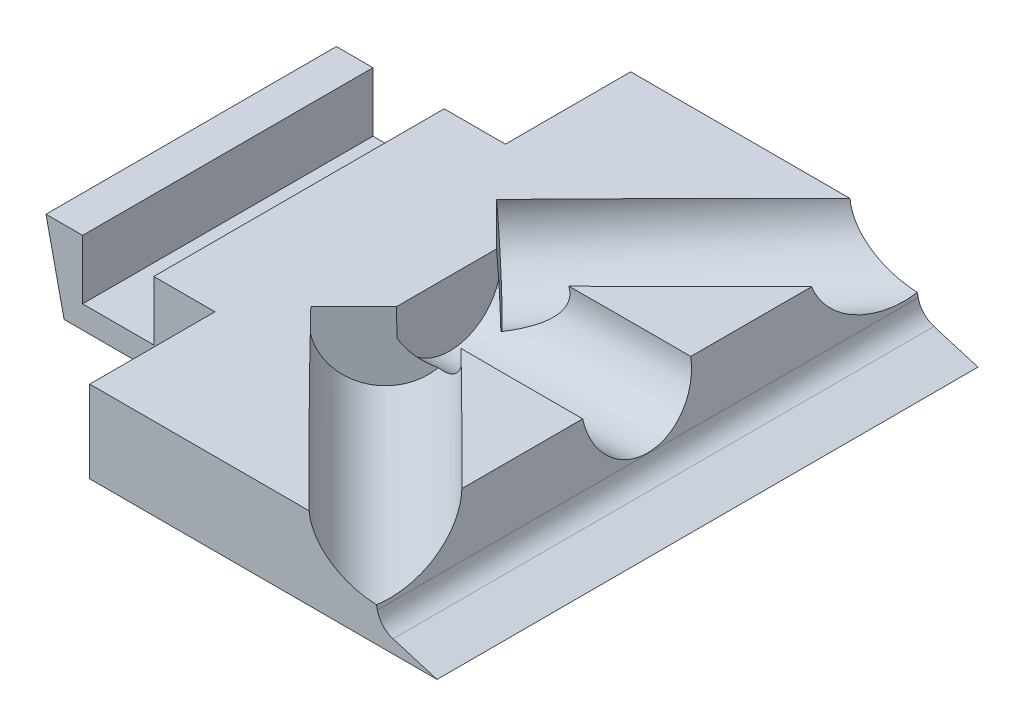
SolidWorks part; units mm, degrees
ref_plane "Front Plane" through (0, 0, 0) normal (0, 0, 1) x (1, 0, 0)
ref_plane "Top Plane" through (0, 0, 0) normal (0, 1, 0) x (1, 0, 0)
ref_plane "Right Plane" through (0, 0, 0) normal (1, 0, 0) x (0, 0, -1)
sketch "Sketch1" plane through (0, 0, 0) normal (0, 1, 0) x (1, 0, 0)
  line L1 (-55.9466, 49.5438) -> (39.0534, 49.5438)
  line L2 (-55.9466, 49.5438) -> (-55.9466, -45.4562)
  line L3 (-55.9466, -45.4562) -> (39.0534, -45.4562)
  line L4 (39.0534, 49.5438) -> (39.0534, -45.4562)
  dimension "D1" = 95
  dimension "D2" = 95
extrude "Boss-Extrude1" add sketch "Sketch1" along normal blind 50
sketch "Sketch2" plane through (0, 0, 45.4562) normal (0, 0, 1) x (1, 0, 0)
  line L0 (39.0534, 0) -> (36.3534, 50)
  line L1 (-55.9466, 50) -> (39.0534, 50) construction
  line L2 (36.3534, 50) -> (39.0534, 50)
  line L3 (39.0534, 50) -> (39.0534, 0)
  dimension "D1" = 2.7
extrude "Cut-Extrude1" cut sketch "Sketch2" against normal blind 100
sketch "Sketch3" plane through (38.9399, 2.1028, 0) normal (0.9985, 0.0539, 0) x (0, 0, -1)
  line L0 (-45.4562, 47.967) -> (-45.4562, -2.1058) construction
  line L1 (-45.4562, -2.1058) -> (49.5438, -2.1058) construction
  circle A0 centre (2.0438, 13.3942) radius 9.5
  point P4 (2.0438, -2.1058)
  dimension "D3" = 19
  dimension "D1" = 47.5
  dimension "D2" = 15.5
extrude "Cut-Extrude2" cut sketch "Sketch3" against normal blind 45
sketch "Sketch5" plane through (0, 50, 0) normal (0, 1, 0) x (1, 0, 0)
  line L0 (39.0534, 49.5438) -> (39.0534, 29.5438)
  line L1 (39.0534, -45.4562) -> (39.0534, 49.5438) construction
  line L2 (39.0534, 29.5438) -> (19.0534, 49.5438)
  line L3 (19.0534, 49.5438) -> (39.0534, 49.5438)
  line L4 (39.0534, -45.4562) -> (39.0534, -25.4562)
  line L5 (39.0534, -25.4562) -> (19.0534, -45.4562)
  line L6 (-55.9466, -45.4562) -> (36.3534, -45.4562) construction
  line L7 (19.0534, -45.4562) -> (39.0534, -45.4562)
  dimension "D1" = 20
  dimension "D2" = 20
  dimension "D3" = 20
  dimension "D4" = 20
extrude "Cut-Extrude4" cut sketch "Sketch5" against normal blind 45
sketch "Sketch6" plane through (0, 50, 0) normal (0, 1, 0) x (1, 0, 0)
  line L0 (19.0534, -45.4562) -> (12.9256, -39.3283)
  line L1 (12.9256, -39.3283) -> (6.7977, -45.4562)
  line L2 (-55.9466, -45.4562) -> (19.0534, -45.4562) construction
  line L3 (6.7977, -45.4562) -> (19.0534, -45.4562)
  line L4 (19.0534, 49.5438) -> (12.9256, 43.4159)
  line L5 (12.9256, 43.4159) -> (6.7977, 49.5438)
  line L6 (19.0534, 49.5438) -> (-55.9466, 49.5438) construction
  line L7 (6.7977, 49.5438) -> (19.0534, 49.5438)
extrude "Cut-Extrude5" cut sketch "Sketch6" against normal blind 45
sketch "Sketch7" plane through (-13.2014, 0, 13.2014) normal (-0.7071, 0, 0.7071) x (0.7071, 0, 0.7071)
  line L0 (45.6152, 5) -> (42.9152, 50)
  line L1 (45.6152, 50) -> (36.9491, 50) construction
  line L2 (42.9152, 50) -> (45.6152, 50)
  line L3 (45.6152, 50) -> (45.6152, 5)
  dimension "D1" = 2.7
extrude "Cut-Extrude6" cut sketch "Sketch7" against normal blind 45
sketch "Sketch8" plane through (-15.2452, 0, -15.2452) normal (-0.7071, 0, -0.7071) x (-0.7071, 0, 0.7071)
  line L0 (-48.5056, 5) -> (-45.8056, 50)
  line L1 (-39.8395, 50) -> (-48.5056, 50) construction
  line L2 (-45.8056, 50) -> (-48.5056, 50)
  line L3 (-48.5056, 50) -> (-48.5056, 5)
  dimension "D1" = 2.7
extrude "Cut-Extrude7" cut sketch "Sketch8" against normal blind 45
sketch "Sketch9" plane through (34.387, 2.9178, -34.387) normal (0.7058, 0.0599, -0.7058) x (-0.7084, 0.0597, -0.7033)
  line L1 (-6.2064, 2.4614) -> (-2.7761, 47.4176) construction
  line L2 (7.1802, -4.1889) -> (74.4757, -4.1889) construction
  circle A0 centre (14.527, 11.3111) radius 9.5
  point P6 (7.9302, 14.2331)
  dimension "D1" = 15.5
  dimension "D2" = 20
extrude "Cut-Extrude9" cut sketch "Sketch9" against normal blind 45
sketch "Sketch11" plane through (32.3505, 2.745, 32.3505) normal (0.7058, 0.0599, 0.7058) x (0.7033, 0.0597, -0.7084)
  line L0 (11.3114, 46.7473) -> (9.3514, 1.703) construction
  line L1 (-71.5478, 4.7302) -> (-4.7333, -3.3019) construction
  circle A0 centre (-10.1775, 12.9642) radius 9.5
  dimension "D1" = 20
  dimension "D2" = 15.5
extrude "Cut-Extrude10" cut sketch "Sketch11" against normal blind 45
sketch "Sketch12" plane through (0, 5, 0) normal (0, 1, 0) x (1, 0, 0)
  line L1 (38.7834, -45.4562) -> (6.7977, -45.4562)
  line L2 (38.7834, -45.4562) -> (38.7834, 49.5438)
  line L3 (38.7834, 49.5438) -> (6.7977, 49.5438)
  line L4 (6.7977, -45.4562) -> (6.7977, 49.5438)
extrude "Boss-Extrude2" add sketch "Sketch12" along normal blind 45
sketch "Sketch13" plane through (0, 0, 45.4562) normal (0, 0, 1) x (1, 0, 0)
  line L0 (39.0534, 0) -> (29.0534, 3)
  line L1 (29.0534, 3) -> (19.0534, 50)
  line L2 (-55.9466, 50) -> (38.7834, 50) construction
  line L3 (19.0534, 50) -> (49.7453, 50)
  line L4 (49.7453, 50) -> (39.0534, 0)
  line L5 (-55.9466, 0) -> (39.0534, 0) construction
  dimension "D1" = 10
  dimension "D2" = 3
  dimension "D3" = 10
extrude "Cut-Extrude11" cut sketch "Sketch13" against normal blind 100
sketch "Sketch14" plane through (-5.9946, -0.3237, 0) normal (0.9985, 0.0539, 0) x (0, 0, -1)
  circle A0 centre (2.0438, 13.3942) radius 9.5
extrude "Cut-Extrude12" cut sketch "Sketch14" along normal blind 100
sketch "Sketch15" plane through (0.5878, 0.0499, 0.5878) normal (0.7058, 0.0599, 0.7058) x (0.7033, 0.0597, -0.7084)
  circle A0 centre (-10.1775, 12.9642) radius 9.5
extrude "Cut-Extrude13" cut sketch "Sketch15" along normal blind 100
sketch "Sketch16" plane through (2.6243, 0.2227, -2.6243) normal (0.7058, 0.0599, -0.7058) x (-0.7084, 0.0597, -0.7033)
  circle A0 centre (14.527, 11.3111) radius 9.5
extrude "Cut-Extrude14" cut sketch "Sketch16" along normal blind 100
fillet "Fillet2" radius 4 1 edges at (29.0534, 3, -2.0438)
sketch "Sketch17" plane through (0, 0, 45.4562) normal (0, 0, 1) x (1, 0, 0)
  line L3 (-55.9466, 0) -> (-21.9466, 0)
  line L4 (-55.9466, 0) -> (-55.9466, 34)
  line L5 (-55.9466, 34) -> (-21.9466, 34)
  line L6 (-21.9466, 0) -> (-21.9466, 34)
  dimension "D1" = 34
  dimension "D2" = 34
extrude "Cut-Extrude16" cut sketch "Sketch17" against normal blind 22
sketch "Sketch19" plane through (0, 0, -49.5438) normal (0, 0, -1) x (-1, 0, 0)
  line L1 (55.9466, 0) -> (21.9466, 0)
  line L2 (55.9466, 0) -> (55.9466, 34)
  line L3 (55.9466, 34) -> (21.9466, 34)
  line L4 (21.9466, 0) -> (21.9466, 34)
  dimension "D1" = 34
  dimension "D2" = 34
extrude "Cut-Extrude17" cut sketch "Sketch19" against normal blind 22
sketch "Sketch20" plane through (0, 0, 23.4562) normal (0, 0, 1) x (1, 0, 0)
  line L0 (-55.9466, 0) -> (-21.9466, 0) construction
  line L1 (-45.1966, 20.5) -> (-32.6966, 20.5)
  line L2 (-45.1966, 20.5) -> (-45.1966, 4)
  line L3 (-45.1966, 4) -> (-32.6966, 4)
  line L4 (-32.6966, 20.5) -> (-32.6966, 4)
  line L5 (-55.9466, 34) -> (-55.9466, 0) construction
  line L6 (-21.9466, 0) -> (-21.9466, 34) construction
  dimension "D1" = 12.5
  dimension "D2" = 16.5
  dimension "D3" = 4
  dimension "D4" = 10.75
  dimension "D5" = 10.75
extrude "Cut-Extrude18" cut sketch "Sketch20" against normal blind 60
sketch "Sketch21" plane through (0, 0, 23.4562) normal (0, 0, 1) x (1, 0, 0)
  line L0 (-55.9466, 34) -> (-48.4466, 0)
  line L1 (-55.9466, 0) -> (-21.9466, 0) construction
  line L2 (-48.4466, 0) -> (-55.9466, 0)
  line L3 (-55.9466, 0) -> (-55.9466, 34)
  dimension "D1" = 7.5
extrude "Cut-Extrude19" cut sketch "Sketch21" against normal blind 60
sketch "Sketch22" plane through (0, 0, 45.4562) normal (0, 0, 1) x (1, 0, 0)
  line L0 (16.5817, 14.4177) -> (-57.7624, 14.4177)
  line L1 (-57.7624, 14.4177) -> (-57.7624, 55.8779)
  line L2 (-57.7624, 55.8779) -> (42.054, 55.8779)
  line L3 (42.054, 55.8779) -> (42.054, 14.4177)
  line L4 (42.054, 14.4177) -> (16.5817, 14.4177)
  ellipse E0 centre (29.9926, 15.5557) end of major axis (16.5817, 14.4177) minor radius 9.5 (24.5777, 24.0358) -> (28.4071, 6.0379) ccw construction
extrude "Cut-Extrude20" cut sketch "Sketch22" against normal blind 100
